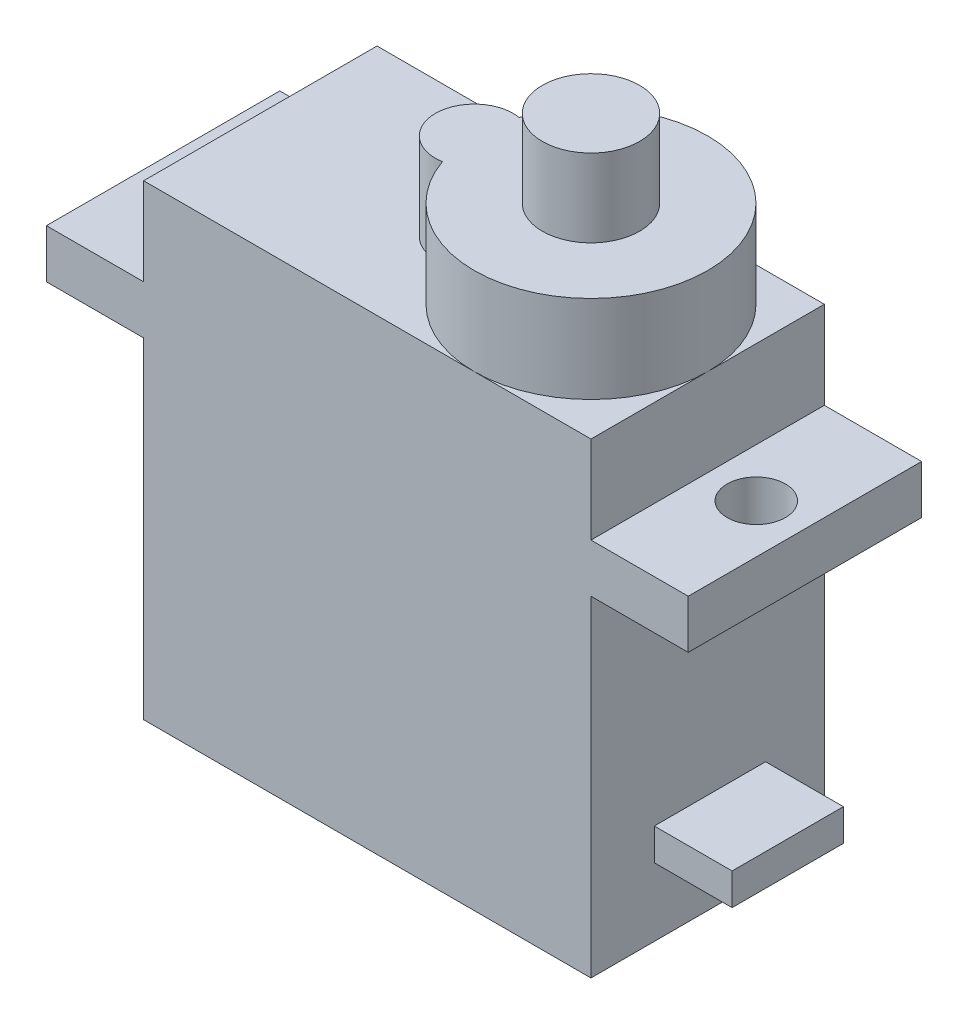
SolidWorks part; units mm, degrees
ref_plane "Front Plane" through (0, 0, 0) normal (0, 0, 1) x (1, 0, 0)
ref_plane "Top Plane" through (0, 0, 0) normal (0, 1, 0) x (1, 0, 0)
ref_plane "Right Plane" through (0, 0, 0) normal (1, 0, 0) x (0, 0, -1)
sketch "Sketch2" plane through (0, 0, 0) normal (0, 1, 0) x (1, 0, 0)
  line L1 (-11.5973, 4.7673) -> (11.4027, 4.7673)
  line L2 (-11.5973, 4.7673) -> (-11.5973, -7.2327)
  line L3 (-11.5973, -7.2327) -> (11.4027, -7.2327)
  line L4 (11.4027, 4.7673) -> (11.4027, -7.2327)
  dimension "D1" = 23
  dimension "D2" = 12
extrude "Boss-Extrude1" add sketch "Sketch2" along normal blind 24
sketch "Sketch3" plane through (0, 24, 0) normal (0, 1, 0) x (1, 0, 0)
  line L0 (11.4027, -1.2327) -> (5.4027, -1.2327) construction
  line L1 (11.4027, -7.2327) -> (11.4027, 4.7673) construction
  line L2 (11.4027, -1.2327) -> (11.4027, 4.7673) construction
  line L3 (5.4027, -1.2327) -> (-2.5973, -1.2327) construction
  arc A0 (-0.264, -3.2047) -> (-0.264, 0.7394) centre (5.4027, -1.2327) ccw
  arc A1 (-0.264, 0.7394) -> (-0.264, -3.2047) centre (-0.5973, -1.2327) ccw
  dimension "D1" = 14
extrude "Boss-Extrude2" add sketch "Sketch3" along normal blind 4.5
sketch "Sketch4" plane through (0, 28.5, 0) normal (0, 1, 0) x (1, 0, 0)
  circle A0 centre (5.4027, -1.2327) radius 2.5
  dimension "D1" = 5
extrude "Boss-Extrude3" add sketch "Sketch4" along normal blind 4
sketch "Sketch5" plane through (11.4027, 0, 0) normal (1, 0, 0) x (0, 0, -1)
  line L0 (-7.2327, 24) -> (-7.2327, 19.5) construction
  line L1 (-7.2327, 24) -> (-7.2327, 0) construction
  line L2 (-7.2327, 19.5) -> (-7.2327, 17) construction
  line L3 (4.7673, 24) -> (4.7673, 0) construction
  line L4 (-7.2327, 19.5) -> (4.7673, 19.5)
  line L5 (-7.2327, 19.5) -> (-7.2327, 17)
  line L6 (-7.2327, 17) -> (4.7673, 17)
  line L7 (4.7673, 19.5) -> (4.7673, 17)
  dimension "D1" = 4.5
  dimension "D2" = 2.5
extrude "Boss-Extrude4" add sketch "Sketch5" along normal blind 5
sketch "Sketch6" plane through (-11.5973, 0, 0) normal (-1, 0, 0) x (0, 0, 1)
  line L0 (-4.7673, 24) -> (-4.7673, 19.5) construction
  line L1 (-4.7673, 24) -> (-4.7673, 0) construction
  line L2 (-4.7673, 19.5) -> (-4.7673, 17) construction
  line L4 (-4.7673, 19.5) -> (7.2327, 19.5)
  line L5 (-4.7673, 19.5) -> (-4.7673, 17)
  line L6 (-4.7673, 17) -> (7.2327, 17)
  line L7 (7.2327, 19.5) -> (7.2327, 17)
  dimension "D1" = 4.5
  dimension "D2" = 2.5
extrude "Boss-Extrude5" add sketch "Sketch6" along normal blind 5
sketch "Sketch7" plane through (0, 19.5, 0) normal (0, 1, 0) x (1, 0, 0)
  circle A0 centre (-14.0973, -1.2327) radius 1.5
  circle A1 centre (13.9027, -1.2327) radius 1.5
  dimension "D1" = 3
  dimension "D2" = 3
extrude "Cut-Extrude1" cut sketch "Sketch7" against normal blind 5
sketch "Sketch8" plane through (11.4027, 0, 0) normal (1, 0, 0) x (0, 0, -1)
  line L1 (-3.9774, 3.5043) -> (1.7457, 3.5043)
  line L2 (-3.9774, 3.5043) -> (-3.9774, 5.1395)
  line L3 (-3.9774, 5.1395) -> (1.7457, 5.1395)
  line L4 (1.7457, 3.5043) -> (1.7457, 5.1395)
extrude "Boss-Extrude6" add sketch "Sketch8" along normal blind 4
